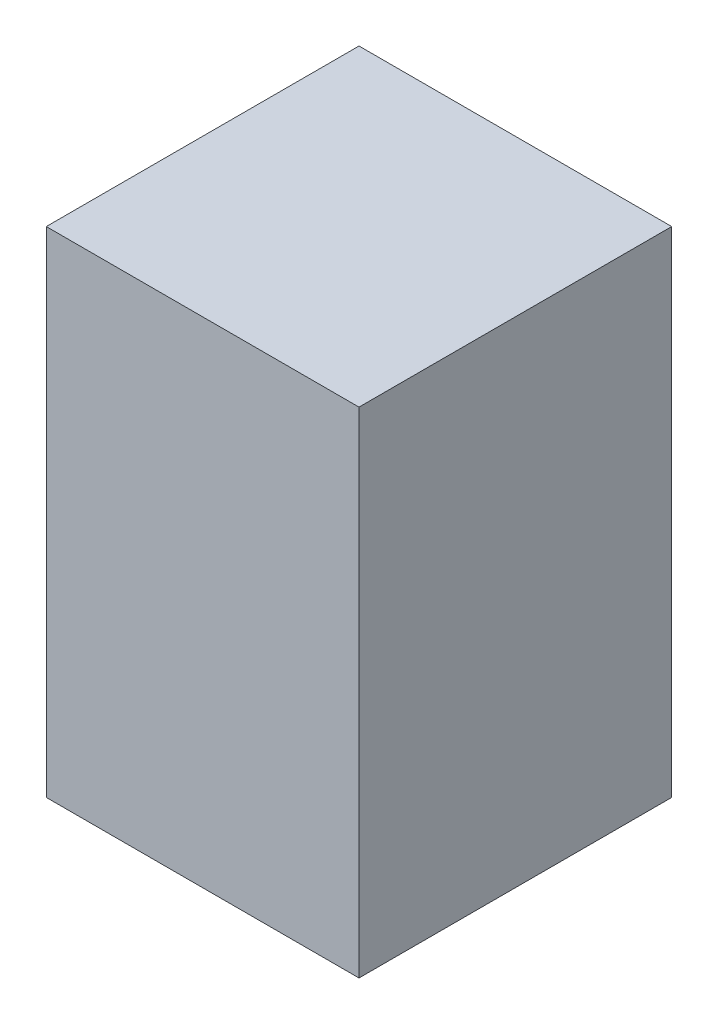
SolidWorks part; units mm, degrees
ref_plane "Front Plane" through (0, 0, 0) normal (0, 0, 1) x (1, 0, 0)
ref_plane "Top Plane" through (0, 0, 0) normal (0, 1, 0) x (1, 0, 0)
ref_plane "Right Plane" through (0, 0, 0) normal (1, 0, 0) x (0, 0, -1)
sketch "Sketch1" plane through (0, 0, 0) normal (0, 1, 0) x (1, 0, 0)
  line L1 (6.325, -6.325) -> (-6.325, -6.325)
  line L2 (6.325, -6.325) -> (6.325, 6.325)
  line L3 (6.325, 6.325) -> (-6.325, 6.325)
  line L4 (-6.325, -6.325) -> (-6.325, 6.325)
  line L5 (6.325, -6.325) -> (-6.325, 6.325) construction
  line L6 (6.325, 6.325) -> (-6.325, -6.325) construction
  point P0 (0, 0)
  dimension "D1" = 12.65
extrude "Boss-Extrude1" add sketch "Sketch1" along normal blind 20
